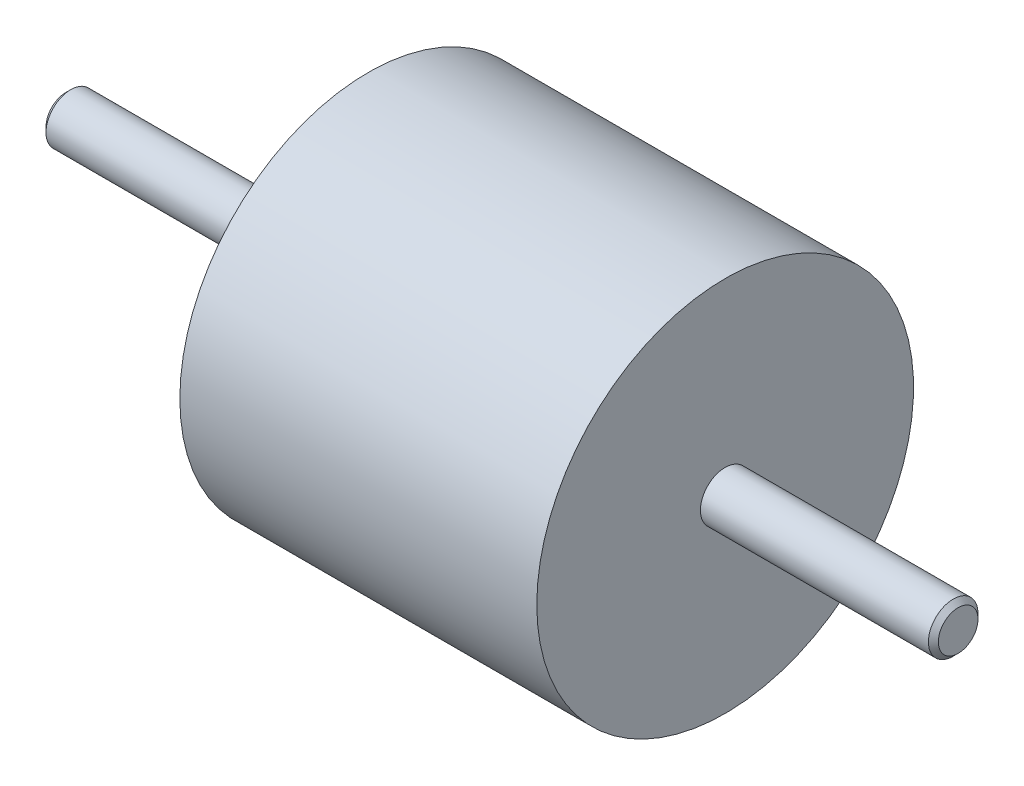
SolidWorks part; units mm, degrees
ref_plane "Face" through (0, 0, 0) normal (0, 0, 1) x (1, 0, 0)
ref_plane "Dessus" through (0, 0, 0) normal (0, 1, 0) x (1, 0, 0)
ref_plane "Droite" through (0, 0, 0) normal (1, 0, 0) x (0, 0, -1)
sketch "Esquisse1" plane through (0, 0, 0) normal (0, 0, 1) x (1, 0, 0)
  line L0 (-33.3365, -19.3923) -> (2.6635, -19.3923)
  line L1 (26.1635, -35.8923) -> (26.1635, -38.3923)
  line L2 (26.1635, -38.3923) -> (-63.8365, -38.3923)
  line L3 (-63.8365, -38.3923) -> (-63.8365, -35.8923)
  line L4 (-107.1513, -38.3923) -> (60.2006, -38.3923) construction
  line L5 (-33.3365, -19.3923) -> (-33.3365, -35.8923)
  line L6 (-33.3365, -35.8923) -> (-63.8365, -35.8923)
  line L10 (26.1635, -35.8923) -> (2.6635, -35.8923)
  line L11 (2.6635, -35.8923) -> (2.6635, -19.3923)
revolve "Révolution1" add sketch "Esquisse1" angle 360 about L4
chamfer "Chanfrein1" distance 0.5 angle 45
